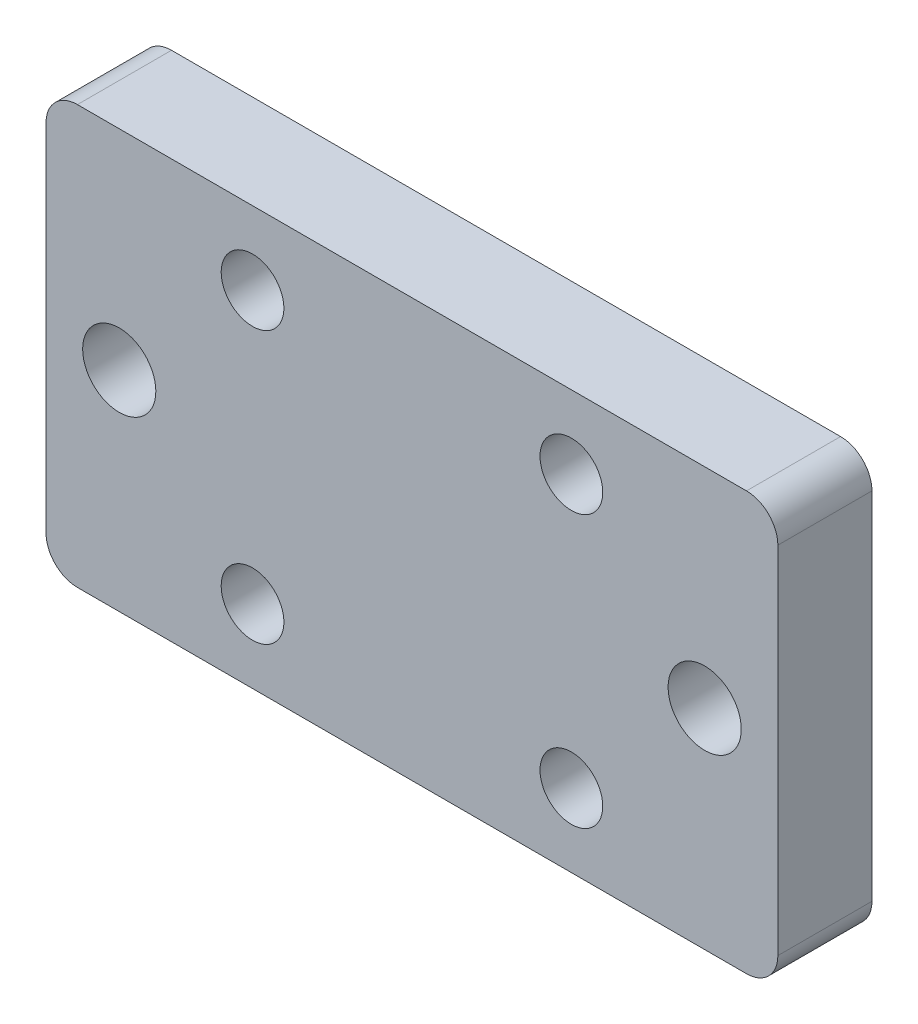
SolidWorks part; units mm, degrees
ref_plane "Plan de face" through (0, 0, 0) normal (0, 0, 1) x (1, 0, 0)
ref_plane "Plan de dessus" through (0, 0, 0) normal (0, 1, 0) x (1, 0, 0)
ref_plane "Plan de droite" through (0, 0, 0) normal (1, 0, 0) x (0, 0, -1)
sketch "Esquisse1" plane through (0, 0, 0) normal (0, 0, 1) x (1, 0, 0)
  line L1 (0, 0) -> (70, 0)
  line L2 (0, 0) -> (0, 40)
  line L3 (0, 40) -> (70, 40)
  line L4 (70, 0) -> (70, 40)
  dimension "D1" = 70
  dimension "D2" = 40
extrude "Boss.-Extru.1" add sketch "Esquisse1" along normal blind 9
sketch "Esquisse2" plane through (0, 0, 9) normal (0, 0, 1) x (1, 0, 0)
  line L0 (35, 0) -> (35, 40) construction
  line L1 (0, 0) -> (70, 0) construction
  line L2 (70, 40) -> (0, 40) construction
  line L3 (35, 20) -> (0, 20) construction
  line L4 (0, 40) -> (0, 0) construction
  circle A0 centre (19.75, 33) radius 3
  circle A1 centre (50.25, 33) radius 3
  circle A2 centre (50.25, 7) radius 3
  circle A3 centre (19.75, 7) radius 3
  circle A4 centre (7, 20) radius 3.5
  circle A5 centre (63, 20) radius 3.5
  dimension "D1" = 30.5
  dimension "D2" = 26
  dimension "D3" = 6
  dimension "D4" = 7
  dimension "D5" = 56
extrude "Enlèv. mat.-Extru.1" cut sketch "Esquisse2" against normal through all both and the other way through all
fillet "Congé1" radius 3 4 edges at (0, 40, 4.5) (70, 40, 4.5) (70, 0, 4.5) (0, 0, 4.5)
